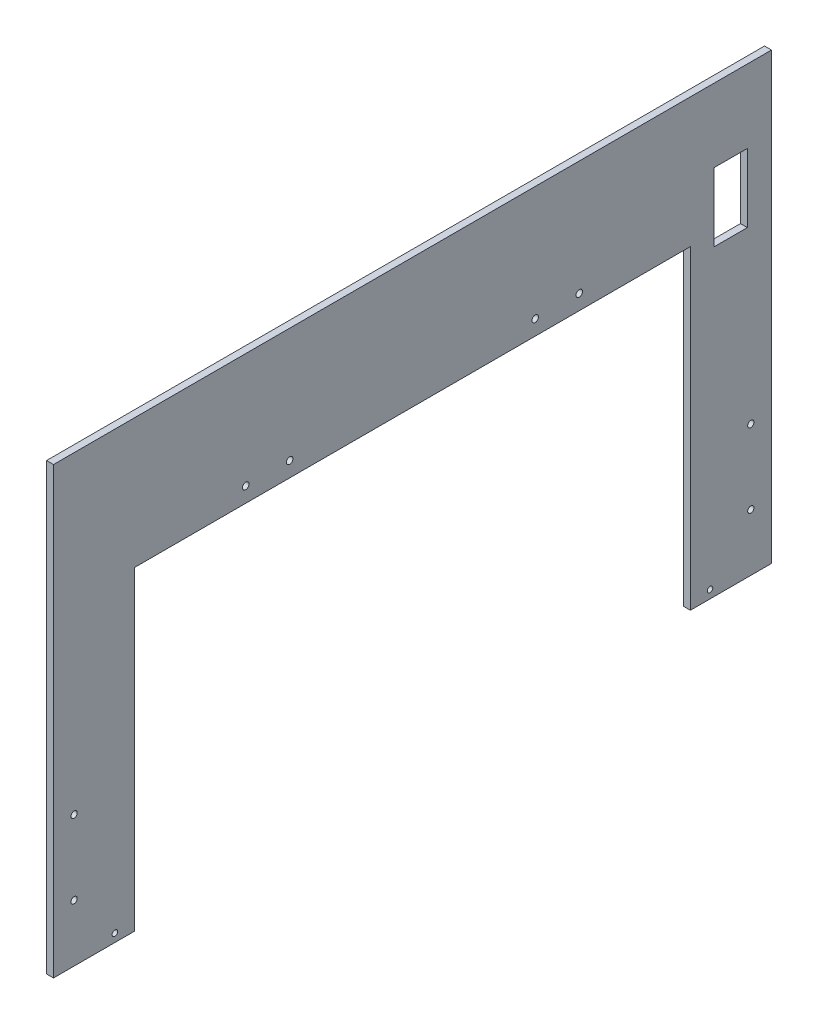
SolidWorks part; units mm, degrees
ref_plane "Front Plane" through (0, 0, 0) normal (0, 0, 1) x (1, 0, 0)
ref_plane "Top Plane" through (0, 0, 0) normal (0, 1, 0) x (1, 0, 0)
ref_plane "Right Plane" through (0, 0, 0) normal (1, 0, 0) x (0, 0, -1)
sketch "Sketch1" plane through (0, 0, 0) normal (1, 0, 0) x (0, 0, -1)
  line L1 (-246.0625, -152.4) -> (246.0625, -152.4)
  line L2 (-246.0625, -152.4) -> (-246.0625, 152.4)
  line L3 (-246.0625, 152.4) -> (246.0625, 152.4)
  line L4 (246.0625, -152.4) -> (246.0625, 152.4)
  line L5 (-246.0625, -152.4) -> (246.0625, 152.4) construction
  line L6 (-246.0625, 152.4) -> (246.0625, -152.4) construction
  point P0 (0, 0)
  dimension "D1" = 304.8
  dimension "D2" = 492.125
extrude "Boss-Extrude1" add sketch "Sketch1" along normal blind 4.7625
sketch "Sketch2" plane through (4.7625, 0, 0) normal (1, 0, 0) x (0, 0, -1)
  line L0 (0, 0) -> (42.4264, 42.4264) construction
  line L1 (-24.8528, -60) -> (24.8528, -60)
  line L2 (-60, -24.8528) -> (-60, 24.8528)
  line L3 (-24.8528, 60) -> (24.8528, 60)
  line L4 (60, -24.8528) -> (60, 24.8528)
  line L5 (-42.4264, -42.4264) -> (42.4264, 42.4264) construction
  line L6 (0, 0) -> (-42.4264, 42.4264) construction
  line L7 (-42.4264, 42.4264) -> (-24.8528, 60) construction
  line L8 (0, 0) -> (42.4264, -42.4264) construction
  line L9 (-42.4264, 42.4264) -> (-60, 24.8528) construction
  line L10 (42.4264, -42.4264) -> (24.8528, -60) construction
  line L11 (42.4264, -42.4264) -> (60, -24.8528) construction
  line L12 (0, 0) -> (0, 60) construction
  line L13 (0, 0) -> (0, -60) construction
  line L14 (42.4264, 42.4264) -> (60, 24.8528) construction
  line L15 (42.4264, 42.4264) -> (24.8528, 60) construction
  line L16 (-42.4264, -42.4264) -> (-24.8528, -60) construction
  line L17 (-42.4264, -42.4264) -> (-60, -24.8528) construction
  line L18 (-24.8528, 60) -> (-60, 24.8528)
  line L19 (24.8528, 60) -> (60, 24.8528)
  line L20 (42.4264, -42.4264) -> (60, -24.8528)
  line L21 (24.8528, -60) -> (42.4264, -42.4264)
  line L22 (-60, -24.8528) -> (-24.8528, -60)
  point P0 (0, 0)
  dimension "D2" = 60
extrude "Cut-Extrude1" cut sketch "Sketch2" against normal up to next
sketch "Sketch3" plane through (0, 0, 246.0625) normal (0, 0, 1) x (1, 0, 0)
  line L1 (0, 152.4) -> (4.7625, 152.4)
  line L2 (0, 152.4) -> (0, -152.4)
  line L3 (0, -152.4) -> (4.7625, -152.4)
  line L4 (4.7625, 152.4) -> (4.7625, -152.4)
extrude "Boss-Extrude2" add sketch "Sketch3" against normal up to next
hole_wizard "#8 Clearance Hole1" positions "Sketch5" profile "Sketch4" hole size "#8" standard "ANSI Inch"
sketch "Sketch5" plane through (4.7625, 0, 0) normal (1, 0, 0) x (0, 0, -1)
  line L1 (-246.0625, 152.4) -> (-246.0625, -152.4) construction
  line L2 (-246.0625, -152.4) -> (246.0625, -152.4) construction
  line L3 (246.0625, -152.4) -> (246.0625, 152.4) construction
  point P0 (-231.9337, -113.284)
  point P2 (-231.9337, -62.484)
  point P4 (231.9338, -62.484)
  point P6 (231.9338, -113.284)
  dimension "D1" = 14.1287
  dimension "D2" = 89.916
  dimension "D3" = 39.116
  dimension "D4" = 14.1288
sketch "Sketch4" plane through (4.7625, -113.284, 231.9337) normal (0, 1, 0) x (0, 0, -1)
  line L0 (0, 0) -> (0, 75.7154)
  line L1 (0, 75.7154) -> (2.1526, 74.422)
  line L2 (2.1526, 74.422) -> (2.1526, 0)
  line L5 (2.1526, 0) -> (0, 0)
  line L10 (0, 75.7154) -> (-2.1527, 74.422) construction
  line L11 (0, -6.35) -> (0, 107.95) construction
  dimension "Hole Dia." = 4.3053
  dimension "Hole Depth" = 74.422
  dimension "Drill Angle" = 118
sketch "Sketch9" plane through (4.7625, 0, 0) normal (1, 0, 0) x (0, 0, -1)
  line L0 (-246.0625, -152.4) -> (246.0625, -152.4) construction
  line L1 (-190.5, -152.4) -> (190.5, -152.4)
  line L2 (-190.5, -152.4) -> (-190.5, 63.5)
  line L3 (-190.5, 63.5) -> (190.5, 63.5)
  line L4 (190.5, -152.4) -> (190.5, 63.5)
  point P6 (0, 63.5)
  dimension "D1" = 381
  dimension "D2" = 215.9
extrude "Cut-Extrude2" cut sketch "Sketch9" against normal through all
hole_wizard "#8 Clearance Hole2" positions "Sketch11" profile "Sketch10" hole size "#8" standard "ANSI Inch"
sketch "Sketch11" plane through (4.7625, 0, 0) normal (1, 0, 0) x (0, 0, -1)
  line L0 (-190.5, 63.5) -> (-190.5, -152.4) construction
  line L1 (190.5, -152.4) -> (190.5, 63.5) construction
  line L2 (190.5, 63.5) -> (-190.5, 63.5) construction
  point P0 (-114.3, 73.8188)
  point P2 (-84.1375, 73.8188)
  point P4 (84.1375, 73.8188)
  point P6 (114.3, 73.8188)
  dimension "D1" = 76.2
  dimension "D2" = 30.1625
  dimension "D3" = 30.1625
  dimension "D4" = 76.2
  dimension "D5" = 10.3187
sketch "Sketch10" plane through (4.7625, 73.8188, 114.3) normal (0, 1, 0) x (0, 0, -1)
  line L0 (0, 0) -> (0, 75.7727)
  line L1 (0, 75.7727) -> (2.2479, 74.422)
  line L2 (2.2479, 74.422) -> (2.2479, 0)
  line L5 (2.2479, 0) -> (0, 0)
  line L10 (0, 75.7727) -> (-2.2479, 74.422) construction
  line L11 (0, -6.35) -> (0, 107.95) construction
  dimension "Hole Dia." = 4.4958
  dimension "Hole Depth" = 74.422
  dimension "Drill Angle" = 118
hole_wizard "#6 Clearance Hole1" positions "Sketch13" profile "Sketch12" hole size "#6" standard "ANSI Inch"
sketch "Sketch13" plane through (4.7625, 0, 0) normal (1, 0, 0) x (0, 0, -1)
  line L0 (-246.0625, -152.4) -> (-190.5, -152.4) construction
  line L1 (-190.5, 63.5) -> (-190.5, -152.4) construction
  line L2 (190.5, -152.4) -> (190.5, 63.5) construction
  point P0 (-203.9709, -146.812)
  point P2 (203.9709, -146.812)
  dimension "D1" = 5.588
  dimension "D2" = 13.4709
  dimension "D3" = 13.4709
sketch "Sketch12" plane through (4.7625, -146.812, 203.9709) normal (0, 1, 0) x (0, 0, -1)
  line L0 (0, 0) -> (0, 75.5628)
  line L1 (0, 75.5628) -> (1.8986, 74.422)
  line L2 (1.8986, 74.422) -> (1.8986, 0)
  line L5 (1.8986, 0) -> (0, 0)
  line L10 (0, 75.5628) -> (-1.8987, 74.422) construction
  line L11 (0, -6.35) -> (0, 107.95) construction
  dimension "Hole Dia." = 3.7973
  dimension "Hole Depth" = 74.422
  dimension "Drill Angle" = 118
sketch "Sketch14" plane through (4.7625, 0, 0) normal (1, 0, 0) x (0, 0, -1)
  line L0 (246.0625, -152.4) -> (246.0625, 152.4) construction
  line L1 (206.6925, 102.235) -> (229.5525, 102.235)
  line L2 (206.6925, 102.235) -> (206.6925, 55.245)
  line L3 (206.6925, 55.245) -> (229.5525, 55.245)
  line L4 (229.5525, 102.235) -> (229.5525, 55.245)
  line L5 (206.6925, 102.235) -> (229.5525, 55.245) construction
  line L6 (206.6925, 55.245) -> (229.5525, 102.235) construction
  line L7 (246.0625, 152.4) -> (-246.0625, 152.4) construction
  point P0 (218.1225, 78.74)
  dimension "D1" = 22.86
  dimension "D2" = 46.99
  dimension "D3" = 27.94
  dimension "D4" = 73.66
extrude "Cut-Extrude3" cut sketch "Sketch14" against normal blind 46.736
